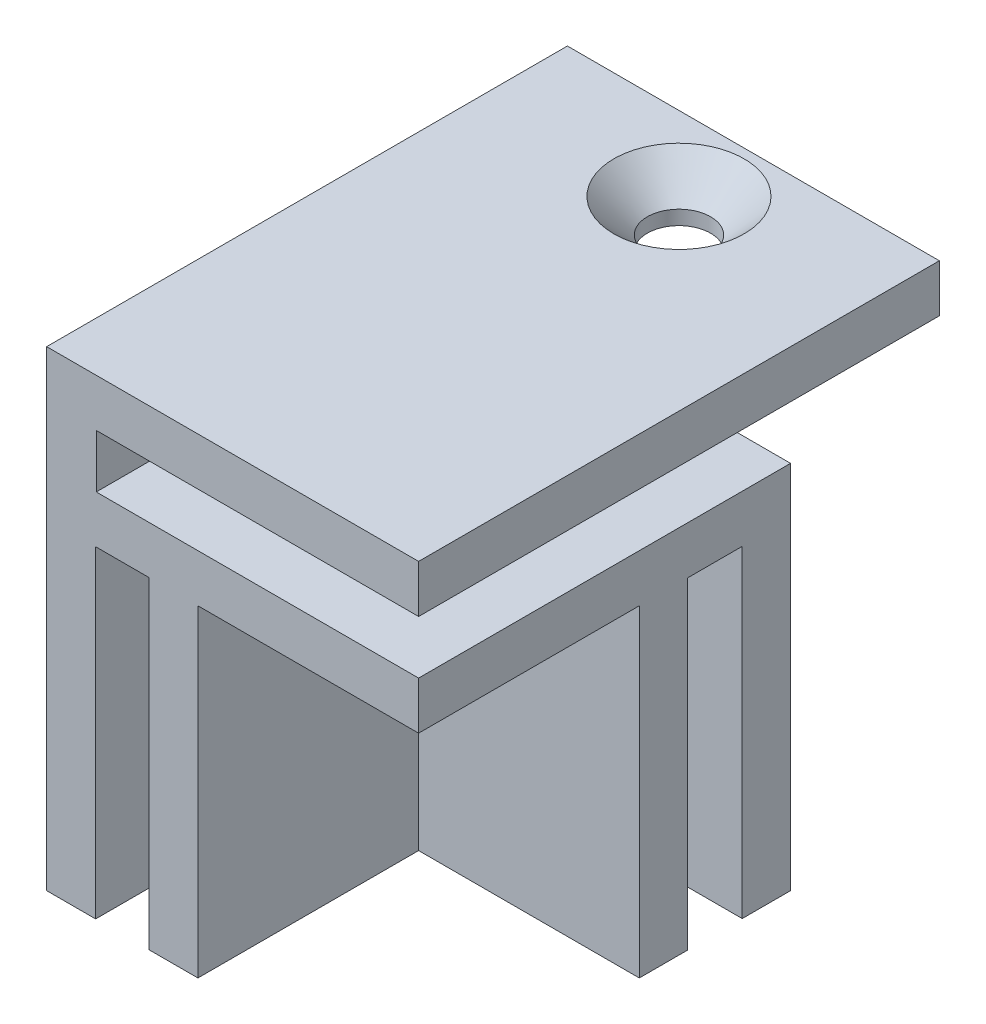
SolidWorks part; units mm, degrees
ref_plane "Plan de face" through (0, 0, 0) normal (0, 0, 1) x (1, 0, 0)
ref_plane "Plan de dessus" through (0, 0, 0) normal (0, 1, 0) x (1, 0, 0)
ref_plane "Plan de droite" through (0, 0, 0) normal (1, 0, 0) x (0, 0, -1)
sketch "Esquisse1" plane through (0, 0, 0) normal (0, 1, 0) x (1, 0, 0)
  line L1 (-35.8867, 13.5315) -> (-5.8867, 13.5315)
  line L2 (-35.8867, 13.5315) -> (-35.8867, -16.4685)
  line L3 (-35.8867, -16.4685) -> (-5.8867, -16.4685)
  line L4 (-5.8867, 13.5315) -> (-5.8867, -16.4685)
  dimension "D1" = 30
  dimension "D2" = 30
extrude "Boss.-Extru.1" add sketch "Esquisse1" along normal blind 38
sketch "Esquisse2" plane through (0, 0, 0) normal (0, -1, 0) x (1, 0, 0)
  line L0 (-5.8867, 16.4685) -> (-5.8867, -13.5315) construction
  line L1 (-5.8867, -9.6315) -> (-23.6867, -9.6315)
  line L2 (-5.8867, -9.6315) -> (-5.8867, -5.2315)
  line L3 (-5.8867, -5.2315) -> (-23.6867, -5.2315)
  line L4 (-23.6867, -9.6315) -> (-23.6867, -5.2315)
  line L5 (-35.8867, 16.4685) -> (-5.8867, 16.4685) construction
  line L6 (-27.6367, 16.4685) -> (-31.9367, 16.4685)
  line L7 (-27.6367, 16.4685) -> (-27.6367, -1.3315)
  line L8 (-27.6367, -1.3315) -> (-31.9367, -1.3315)
  line L9 (-31.9367, 16.4685) -> (-31.9367, -1.3315)
  line L15 (-35.8867, -13.5315) -> (-35.8867, 16.4685) construction
  line L16 (-5.8867, -13.5315) -> (-35.8867, -13.5315) construction
  line L18 (-5.8867, 16.4685) -> (-23.6867, 16.4685)
  line L19 (-5.8867, 16.4685) -> (-5.8867, -1.3315)
  line L20 (-5.8867, -1.3315) -> (-23.6867, -1.3315)
  line L21 (-23.6867, 16.4685) -> (-23.6867, -1.3315)
  dimension "D1" = 4.3
  dimension "D2" = 17.8
  dimension "D3" = 3.95
  dimension "D4" = 4.4
  dimension "D5" = 17.8
  dimension "D6" = 3.9
extrude "Enlèv. mat.-Extru.1" cut sketch "Esquisse2" against normal blind 26
sketch "Esquisse3" plane through (0, 0, 16.4685) normal (0, 0, 1) x (1, 0, 0)
  line L0 (-5.8867, 38) -> (-5.8867, 26) construction
  line L1 (-31.8867, 34.15) -> (-5.8867, 34.15)
  line L2 (-31.8867, 34.15) -> (-31.8867, 29.85)
  line L3 (-31.8867, 29.85) -> (-5.8867, 29.85)
  line L4 (-5.8867, 34.15) -> (-5.8867, 29.85)
  line L5 (-35.8867, 38) -> (-35.8867, 0) construction
  line L6 (-35.8867, 38) -> (-5.8867, 38) construction
  dimension "D1" = 4.3
  dimension "D2" = 4
  dimension "D3" = 3.85
extrude "Enlèv. mat.-Extru.3" cut sketch "Esquisse3" against normal through all
sketch "Esquisse4" plane through (0, 0, -13.5315) normal (0, 0, -1) x (-1, 0, 0)
  line L0 (35.8867, 38) -> (35.8867, 0) construction
  line L1 (5.8867, 38) -> (35.8867, 38)
  line L2 (5.8867, 38) -> (5.8867, 34.15)
  line L3 (5.8867, 34.15) -> (35.8867, 34.15)
  line L4 (35.8867, 38) -> (35.8867, 34.15)
extrude "Boss.-Extru.2" add sketch "Esquisse4" along normal blind 12
sketch "Esquisse7" plane through (0, 38, 0) normal (0, 1, 0) x (1, 0, 0)
  line L0 (-5.8867, -16.4685) -> (-5.8867, 25.5315) construction
  line L1 (-35.8867, 25.5315) -> (-5.8867, 25.5315) construction
  circle A0 centre (-20.8867, 19.5315) radius 5.25
  dimension "D2" = 10.5
  dimension "D1" = 15
  dimension "D3" = 6
hole_wizard "Fraisage pour vis à tête fraisée bombée #51" positions "Esquisse3D2" profile "Esquisse8" countersink size "#5" standard "Ansi Inch" end condition through all
sketch3d "Esquisse3D2"
  point P0 (-20.8867, 38, -19.5315)
sketch "Esquisse8" plane through (-20.8867, 38, -19.5315) normal (1, 0, 0) x (0, 0, 1)
  line L0 (0, 0) -> (0, 38)
  line L1 (0, 38) -> (2.55, 38)
  line L2 (2.55, 38) -> (2.55, 2.7)
  line L3 (2.55, 2.7) -> (5.25, 0)
  line L5 (5.25, 0) -> (0, 0)
  line L6 (-2.55, 2.7) -> (-5.25, 0) construction
  line L11 (0, -6.35) -> (0, 107.95) construction
  dimension "Diamètre du perçage jusqu'au prochain" = 5.1
  dimension "Profondeur du perçage jusqu'au prochain" = 38
  dimension "Diamètre du fraisage entrant" = 10.5
  dimension "Angle du fraisage entrant" = 90
